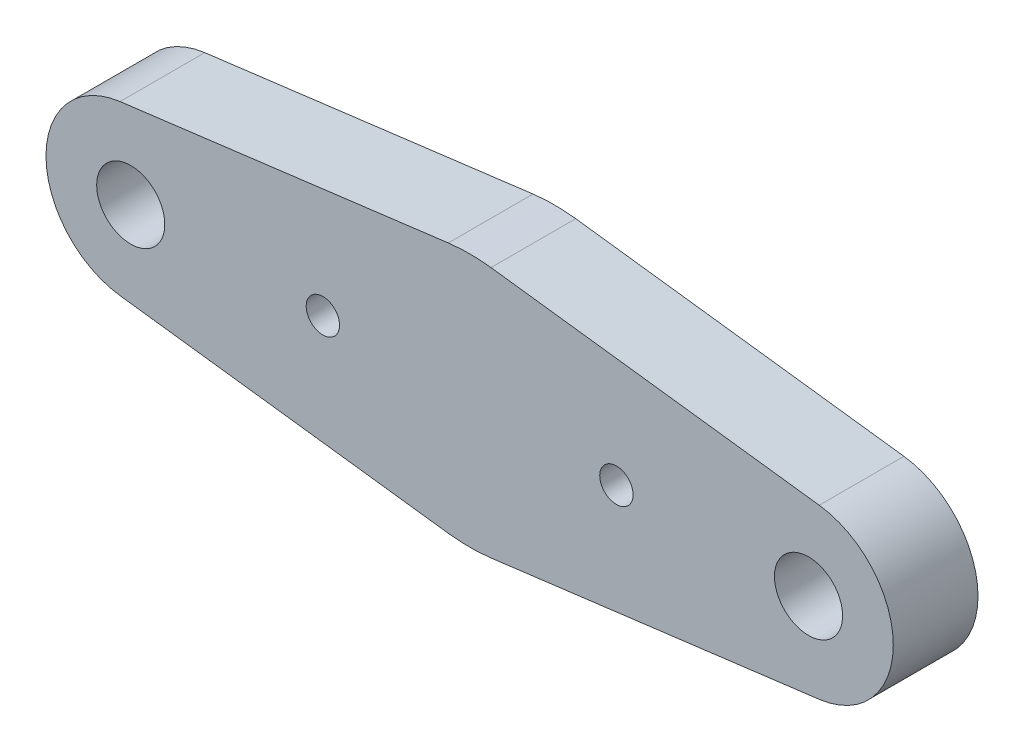
SolidWorks part; units mm, degrees
material "6061-T6 (SS)"
ref_plane "Front" through (0, 0, 0) normal (0, 0, 1) x (1, 0, 0)
ref_plane "Top" through (0, 0, 0) normal (0, 1, 0) x (1, 0, 0)
ref_plane "Right" through (0, 0, 0) normal (1, 0, 0) x (0, 0, -1)
sketch "Sketch1" plane through (0, 0, 0) normal (0, 0, 1) x (1, 0, 0)
  line L0 (1.6002, 9.4238) -> (26.2001, 6.2994)
  line L5 (26.2001, -6.2994) -> (1.6002, -9.4238)
  line L6 (-1.6002, 9.4238) -> (-26.2001, 6.2994)
  line L7 (-26.2001, -6.2994) -> (-1.6002, -9.4238)
  line L8 (25.4, 0) -> (-25.4, 0) construction
  line L9 (0, 3.175) -> (0, -3.175) construction
  arc A1 (26.2001, 6.2994) -> (26.2001, -6.2994) centre (25.4, 0) cw
  arc A2 (-26.2001, 6.2994) -> (-26.2001, -6.2994) centre (-25.4, 0) ccw
  arc A3 (1.6002, 9.4238) -> (-1.6002, 9.4238) centre (0, -3.175) ccw
  arc A4 (1.6002, -9.4238) -> (-1.6002, -9.4238) centre (0, 3.175) cw
  dimension "D1" = 12.7
  dimension "D2" = 6.35
  dimension "D4" = 19.05
  dimension "D3" = 50.8
extrude "Boss-Extrude1" add sketch "Sketch1" along normal blind 6.35
sketch "Sketch4" plane through (0, 0, 0) normal (0, 0, -1) x (-1, 0, 0)
  line L0 (-11, 0) -> (11, 0) construction
  point P0 (-11, 0)
  point P2 (11, 0)
  point P11 (-3.9737, 0.4583)
  dimension "D1" = 22
hole_wizard "M3x0.5 Tapped Hole1" positions "Sketch4" profile "Sketch3" tap size "M3x0.5" standard "ANSI Metric" end condition up to next
sketch "Sketch3" plane through (11, 0, 0) normal (1, 0, 0) x (0, 1, 0)
  line L0 (0, 0) -> (0, 6.35)
  line L1 (0, 6.35) -> (1.25, 6.35)
  line L2 (1.25, 6.35) -> (1.25, 0)
  line L5 (1.25, 0) -> (0, 0)
  line L11 (0, -6.35) -> (0, 107.95) construction
  dimension "Thru Tap Drill Dia." = 2.5
  dimension "Thru Tap Drill Depth" = 6.35
cosmetic thread "Hole Thread1" parameters "D2"=3
cosmetic thread "Hole Thread2" parameters "D2"=3
sketch "Sketch7" plane through (0, 0, 0) normal (0, 0, -1) x (-1, 0, 0)
  point P11 (25.4, 0)
  point P14 (-25.4, 0)
hole_wizard "#10 Clearance Hole1" positions "Sketch7" profile "Sketch6" hole size "#10" standard "ANSI Inch" end condition through all
sketch "Sketch6" plane through (-25.4, 0, 0) normal (1, 0, 0) x (0, 1, 0)
  line L0 (0, 0) -> (0, 6.35)
  line L1 (0, 6.35) -> (2.5527, 6.35)
  line L2 (2.5527, 6.35) -> (2.5527, 0)
  line L5 (2.5527, 0) -> (0, 0)
  line L11 (0, -6.35) -> (0, 107.95) construction
  dimension "Thru Hole Dia." = 5.1054
  dimension "Thru Hole Depth" = 6.35
